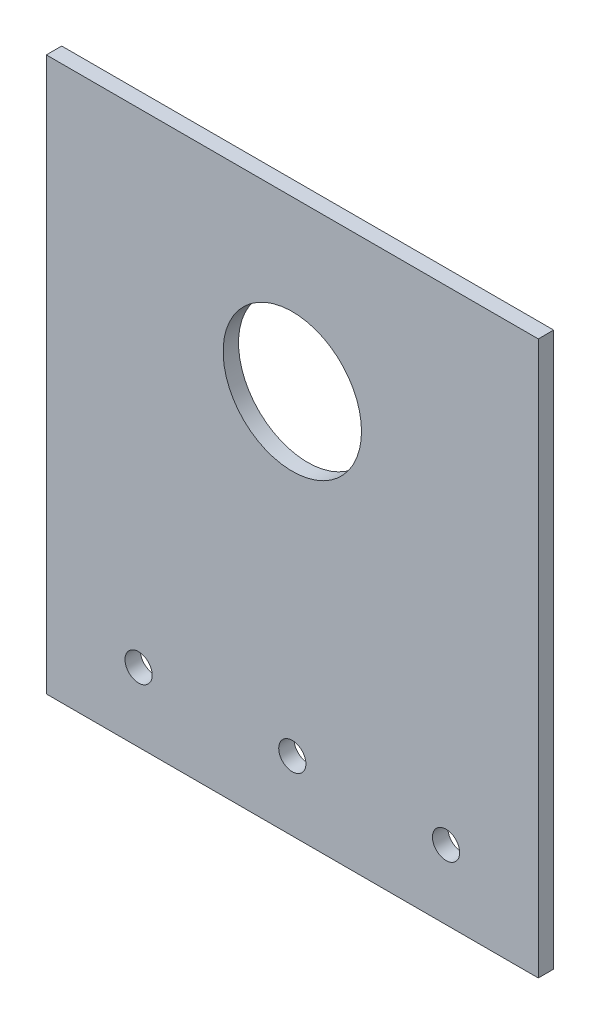
SolidWorks part; units mm, degrees
material "6061-T6 (SS)"
ref_plane "Front Plane" through (0, 0, 0) normal (0, 0, 1) x (1, 0, 0)
ref_plane "Top Plane" through (0, 0, 0) normal (0, 1, 0) x (1, 0, 0)
ref_plane "Right Plane" through (0, 0, 0) normal (1, 0, 0) x (0, 0, -1)
sketch "Sketch1" plane through (0, 0, 0) normal (0, 0, 1) x (1, 0, 0)
  line L1 (-50.8, 57.15) -> (50.8, 57.15)
  line L2 (-50.8, 57.15) -> (-50.8, -57.15)
  line L3 (-50.8, -57.15) -> (50.8, -57.15)
  line L4 (50.8, 57.15) -> (50.8, -57.15)
  line L5 (-50.8, 57.15) -> (50.8, -57.15) construction
  line L6 (-50.8, -57.15) -> (50.8, 57.15) construction
  point P0 (0, 0)
  dimension "D1" = 114.3
  dimension "D2" = 101.6
extrude "Boss-Extrude1" add sketch "Sketch1" along normal blind 3.175
sketch "Sketch2" plane through (0, 0, 3.175) normal (0, 0, 1) x (1, 0, 0)
  line L0 (-50.8, -57.15) -> (50.8, -57.15) construction
  circle A0 centre (0, 22.352) radius 14.2875
  dimension "D1" = 28.575
  dimension "D2" = 79.502
extrude "Cut-Extrude1" cut sketch "Sketch2" against normal blind 3.175 contours A0
hole_wizard "#10 Clearance Hole1" positions "Sketch4" profile "Sketch3" hole size "#10" standard "ANSI Inch" end condition through all
sketch "Sketch4" plane through (0, 0, 3.175) normal (0, 0, 1) x (1, 0, 0)
  line L0 (-50.8, -57.15) -> (50.8, -57.15) construction
  line L1 (-50.8, 57.15) -> (-50.8, -57.15) construction
  line L2 (50.8, -57.15) -> (50.8, 57.15) construction
  point P0 (-31.75, -42.8625)
  point P2 (0, -42.8625)
  point P4 (31.75, -42.8625)
  dimension "D1" = 14.2875
  dimension "D2" = 19.05
  dimension "D3" = 19.05
  dimension "D4" = 50.8
sketch "Sketch3" plane through (-31.75, -42.8625, 3.175) normal (1, 0, 0) x (0, -1, 0)
  line L0 (0, 0) -> (0, 3.175)
  line L1 (0, 3.175) -> (2.8067, 3.175)
  line L2 (2.8067, 3.175) -> (2.8067, 0)
  line L5 (2.8067, 0) -> (0, 0)
  line L11 (0, -6.35) -> (0, 107.95) construction
  dimension "Thru Hole Dia." = 5.6134
  dimension "Thru Hole Depth" = 3.175
